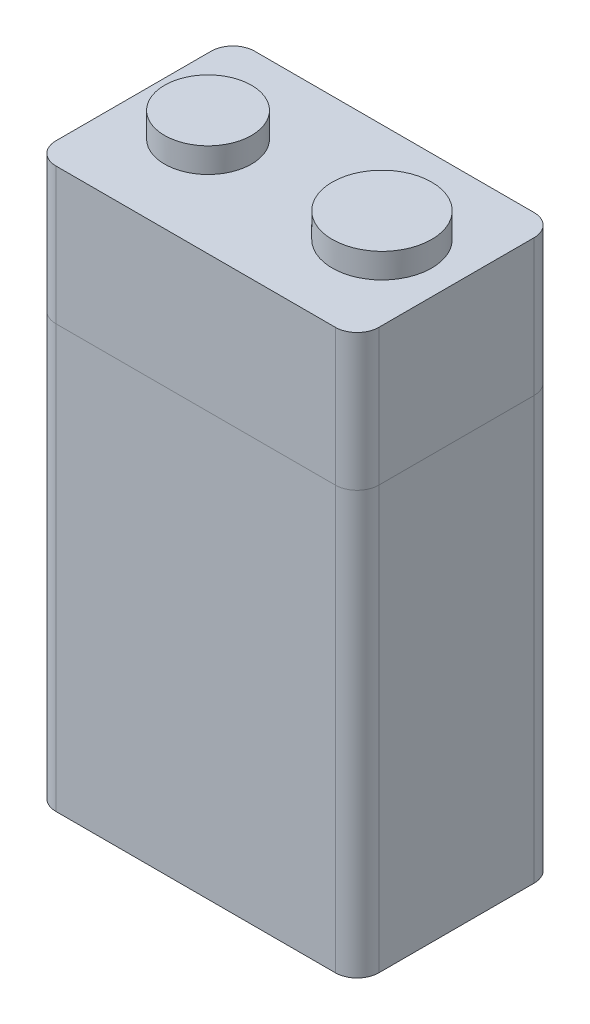
SolidWorks part; units mm, degrees
ref_plane "Front Plane" through (0, 0, 0) normal (0, 0, 1) x (1, 0, 0)
ref_plane "Top Plane" through (0, 0, 0) normal (0, 1, 0) x (1, 0, 0)
ref_plane "Right Plane" through (0, 0, 0) normal (1, 0, 0) x (0, 0, -1)
sketch "Sketch1" plane through (0, 0, 0) normal (0, 1, 0) x (1, 0, 0)
  line L1 (-13, -8) -> (13, -8)
  line L2 (-13, -8) -> (-13, 8)
  line L3 (-13, 8) -> (13, 8)
  line L4 (13, -8) -> (13, 8)
  line L5 (-13, -8) -> (13, 8) construction
  line L6 (-13, 8) -> (13, -8) construction
  point P0 (0, 0)
  dimension "D1" = 26
  dimension "D2" = 16
extrude "Boss-Extrude1" add sketch "Sketch1" along normal blind 45
sketch "Sketch2" plane through (0, 45, 0) normal (0, 1, 0) x (1, 0, 0)
  line L0 (-7, 0) -> (7, 0) construction
  circle A0 centre (-7, 0) radius 3.5
  circle A1 centre (7, 0) radius 4
  point P4 (0, 0)
  dimension "D1" = 7
  dimension "D2" = 8
  dimension "D3" = 14
extrude "Boss-Extrude2" add sketch "Sketch2" along normal blind 2
fillet "Fillet1" radius 1.75 4 edges at (13, 22.5, -8) (13, 22.5, 8) (-13, 22.5, -8) (-13, 22.5, 8)
sketch "Sketch3" plane through (0, 0, 8) normal (0, 0, 1) x (1, 0, 0)
  line L0 (-13, 34) -> (13, 34)
  line L1 (-13, 0) -> (-13, 45) construction
  line L2 (13, 45) -> (13, 0) construction
  line L3 (-11.25, 45) -> (11.25, 45) construction
  dimension "D1" = 11
split line "Split Line1"
